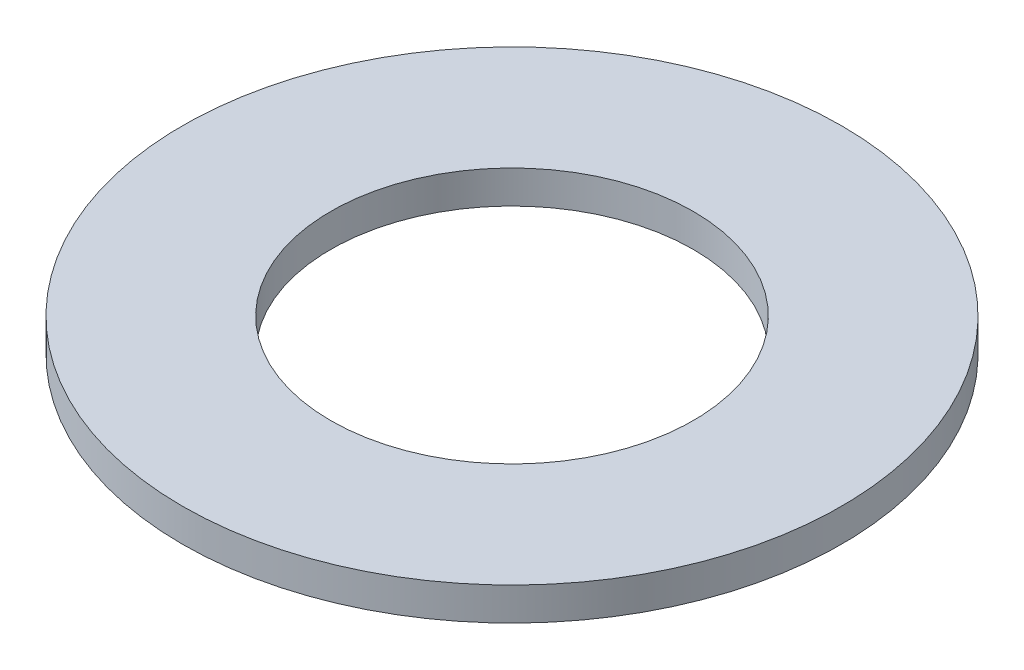
SolidWorks part; units mm, degrees
material "Alloy Steel"
ref_plane "Front Plane" through (0, 0, 0) normal (0, 0, 1) x (1, 0, 0)
ref_plane "Top Plane" through (0, 0, 0) normal (0, 1, 0) x (1, 0, 0)
ref_plane "Right Plane" through (0, 0, 0) normal (1, 0, 0) x (0, 0, -1)
sketch "Sketch1" plane through (0, 0, 0) normal (0, 1, 0) x (1, 0, 0)
  circle A0 centre (0, 0) radius 11
  circle A1 centre (0, 0) radius 20
  dimension "D1" = 22
  dimension "D2" = 40
extrude "Boss-Extrude1" add sketch "Sketch1" along normal blind 2
